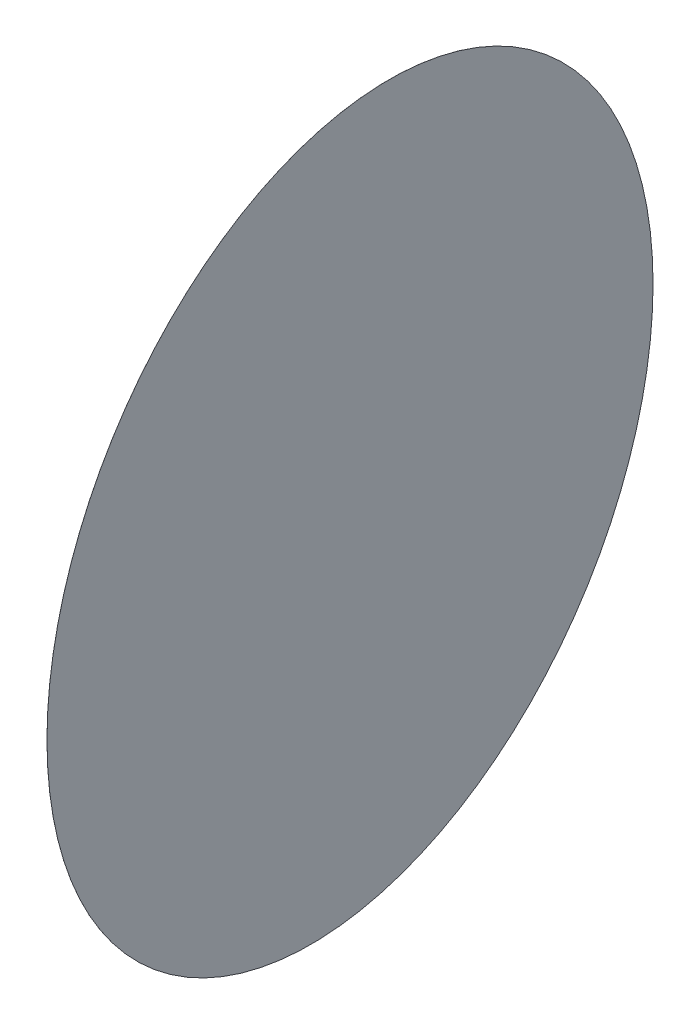
SolidWorks part; units mm, degrees
ref_plane "Front Plane" through (0, 0, 0) normal (0, 0, 1) x (1, 0, 0)
ref_plane "Top Plane" through (0, 0, 0) normal (0, 1, 0) x (1, 0, 0)
ref_plane "Right Plane" through (0, 0, 0) normal (1, 0, 0) x (0, 0, -1)
sketch3d "3DSketch1"
  line L2 (-24.3505, 0, -31.7341) -> (0, 0, 0) construction
  line L3 (0, 0, 0) -> (-15.3073, 0, -36.9552) construction
  line L4 (0, 0, 0) -> (39.6578, 0, -5.221) construction
  line L5 (39.6578, 0, 5.221) -> (0, 0, 0) construction
  line L6 (-15.3073, 0, 36.9552) -> (-2.1567, 4.7319, 42.4023)
  line L7 (-15.3073, 0, 36.9552) -> (0, 0, 0) construction
  line L8 (0, 0, 0) -> (-24.3505, 0, 31.7341) construction
  line L9 (42.285, 0, 78.0778) -> (50.1338, 0, 90.8604)
  line L10 (-24.3505, 0, 31.7341) -> (-35.6431, 4.7319, 23.069)
  line L11 (0, 0, 0) -> (42.8187, 0, 0) construction
  line L12 (-24.3505, 0, -31.7341) -> (-35.6431, 4.7319, -23.069)
  line L13 (-15.3073, 0, -36.9552) -> (-2.1567, 4.7319, -42.4023)
  line L14 (39.6578, 0, -5.221) -> (37.7999, 4.7319, -19.3334)
  line L15 (39.6578, 0, 5.221) -> (37.7999, 4.7319, 19.3334)
  line L16 (30, 40, 0) -> (0, 40, 0) construction
  line L17 (19.2836, 40, 22.9813) -> (0, 40, 0) construction
  line L18 (0, 40, 0) -> (19.2836, 40, -22.9813) construction
  line L19 (10.2606, 40, -28.1908) -> (0, 40, 0) construction
  line L20 (0, 40, 0) -> (-29.5442, 40, -5.2094) construction
  line L21 (-29.5442, 40, 5.2094) -> (0, 40, 0) construction
  line L22 (0, 40, 0) -> (10.2606, 40, 28.1908) construction
  line L23 (77.8401, 0, 43.6828) -> (101.0559, 0, 76.2562)
  line L24 (19.2836, 40, 22.9813) -> (37.7999, 4.7319, 19.3334)
  line L25 (19.2836, 40, -22.9813) -> (37.7999, 4.7319, -19.3334)
  line L26 (10.2606, 40, 28.1908) -> (-2.1567, 4.7319, 42.4023)
  line L27 (-29.5442, 40, 5.2094) -> (-35.6431, 4.7319, 23.069)
  line L28 (-35.6431, 4.7319, -23.069) -> (-29.5442, 40, -5.2094)
  line L29 (-2.1567, 4.7319, -42.4023) -> (10.2606, 40, -28.1908)
  line L30 (39.6578, 0, 5.221) -> (39.6578, 6.5786, 5.221)
  circle A1 centre (0, 0, 0) radius 40
  circle A2 centre (0, 40, 0) radius 30
  point P3 (0, 40, 0)
  point P23 (0, 70, 0)
  dimension "D2" = 15
  dimension "D1" = 80
  dimension "D9" = 60
  dimension "D3" = 15
  dimension "D4" = 15
  dimension "D5" = 105
  dimension "D6" = 105
  dimension "D7" = 15
  dimension "D8" = 7.5
  dimension "D10" = 100
  dimension "D11" = 50
  dimension "D12" = 100
  dimension "D13" = 100
  dimension "D14" = 20
  dimension "D15" = 20
  dimension "D16" = 40
  dimension "D17" = 40
  dimension "D18" = 71.612
sketch3d "3D草图1"
  line L4 (0, 0, 0) -> (58.3341, 0, 0) construction
  line L5 (0, 22.6988, 0) -> (0, -14.0197, 0) construction
  line L6 (0, 0, 0) -> (0, 0, -50000) construction
sketch3d "3D草图2"
  line L0 (19.2836, 40, -22.9813) -> (37.7999, 4.7319, -19.3334) construction
  line L1 (0, 40, 0) -> (19.2836, 40, -22.9813) construction
  line L2 (0, 0, 0) -> (39.6578, 0, -5.221) construction
  line L3 (39.6578, 0, -5.221) -> (37.7999, 4.7319, -19.3334) construction
  line L4 (19.2836, 40, -22.9813) -> (37.7999, 4.7319, -19.3334)
  line L5 (0, 40, 0) -> (19.2836, 40, -22.9813)
  line L6 (0, 0, 0) -> (39.6578, 0, -5.221)
  line L7 (39.6578, 0, -5.221) -> (37.7999, 4.7319, -19.3334)
  line L8 (19.2836, 40, -22.9813) -> (39.6578, 0, -5.221) construction
sketch3d "3D草图3"
  line L0 (0, 0, 0) -> (39.6578, 0, -5.221) construction
sketch "草图1" plane through (39.6578, 0, -5.221) normal (-0.9914, 0, 0.1305) x (0.1305, 0, 0.9914)
  circle A0 centre (0, 0) radius 15
extrude "凸台-拉伸1" add sketch "草图1" against normal blind 0.001
sketch "草图2" plane through (39.6578, 0, -5.221) normal (-0.9914, 0, 0.1305) x (0.1305, 0, 0.9914)
  line L1 (-20.2677, 40) -> (-14.2341, 4.7319) construction
  line L2 (-20.2677, 40) -> (0, 0) construction
  line L3 (-20.2677, 40) -> (-14.2341, 4.7319)
  line L4 (0, 0) -> (-14.2341, 4.7319) construction
  dimension "D1" = 44.741
sketch3d "3D草图4"
  line L0 (19.2836, 40, -22.9813) -> (37.0123, 40, -25.3154) construction
  line L1 (0, 0, 0) -> (39.6578, 0, -5.221) construction
equation "\"servo_angle\"= 15"
equation "\"D2@3DSketch1\"=\"servo_angle\""
equation "\"D3@3DSketch1\"=\"servo_angle\""
equation "\"D4@3DSketch1\"=\"servo_angle\""
equation "\"D5@3DSketch1\"=(360-\"servo_angle\"*3)/3"
equation "\"D6@3DSketch1\"=(360-\"servo_angle\"*3)/3"
equation "\"servo_arm_length\"=15"
equation "\"D7@3DSketch1\"=\"servo_arm_length\""
equation "\"D8@3DSketch1\"=\"servo_angle\"/2"
equation "\"top_diameter\"=60"
equation "\"D9@3DSketch1\"=\"top_diameter\""
equation "\"top_angle\"= 100"
equation "\"D10@3DSketch1\"=\"top_angle\""
equation "\"D11@3DSketch1\"=\"top_angle\"/2"
equation "\"D12@3DSketch1\"=\"top_angle\""
equation "\"D13@3DSketch1\"=\"top_angle\""
equation "\"D14@3DSketch1\"=(360-\"top_angle\"*3)/3"
equation "\"D15@3DSketch1\"=(360-\"top_angle\"*3)/3"
equation "\"leg_length\"=40"
equation "\"D16@3DSketch1\"=\"leg_length\""
equation "\"Base_diameter\"= 80"
equation "\"D1@3DSketch1\"=\"Base_diameter\""
